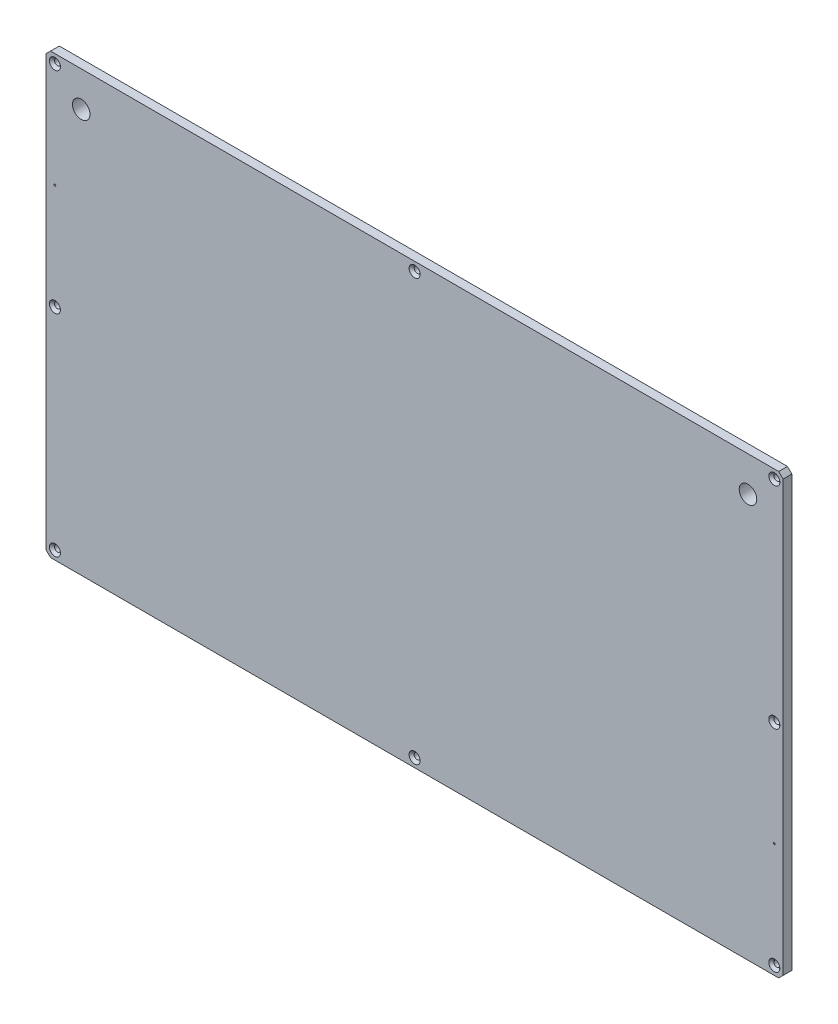
SolidWorks part; units mm, degrees
ref_plane "Front Plane" through (0, 0, 0) normal (0, 0, 1) x (1, 0, 0)
ref_plane "Top Plane" through (0, 0, 0) normal (0, 1, 0) x (1, 0, 0)
ref_plane "Right Plane" through (0, 0, 0) normal (1, 0, 0) x (0, 0, -1)
sketch "Sketch1" plane through (0, 0, 0) normal (0, 0, 1) x (1, 0, 0)
  line L1 (-20, -20) -> (400, -20)
  line L2 (-20, -20) -> (-20, 230)
  line L3 (-20, 230) -> (400, 230)
  line L4 (400, -20) -> (400, 230)
  dimension "D1" = 20
  dimension "D2" = 420
  dimension "D3" = 250
  dimension "D4" = 20
extrude "Boss-Extrude1" add sketch "Sketch1" against normal blind 10
chamfer "Chamfer1" distance 2.5 angle 45 4 edges at (400, 230, -5) (400, -20, -5) (-20, -20, -5) (-20, 230, -5)
ref_plane "Mid X Plane" through (190, 0, 0) normal (-1, 0, 0) x (0, 0, 1)
ref_plane "Mid Y Plane" through (0, 105, 0) normal (0, 1, 0) x (1, 0, 0)
sketch "Sketch8" plane through (0, 0, 0) normal (0, 0, 1) x (1, 0, 0)
  line L0 (400, -17.5) -> (400, 227.5) construction
  line L1 (0, 0) -> (380, 0)
  line L2 (0, 0) -> (0, 210)
  line L3 (0, 210) -> (380, 210)
  line L4 (380, 0) -> (380, 210)
  line L5 (397.5, 230) -> (-17.5, 230) construction
  dimension "D1" = 20
  dimension "D2" = 20
hole_wizard "CSK for M3 Flat Head Machine Screw2" positions "Sketch5" profile "Sketch6" countersink size "M3" standard "ANSI Metric"
sketch "Sketch5" plane through (0, 0, 0) normal (0, 0, 1) x (1, 0, 0)
  line L0 (-17.5, -20) -> (397.5, -20) construction
  line L1 (397.5, 230) -> (-17.5, 230) construction
  line L2 (-20, 227.5) -> (-20, -17.5) construction
  line L3 (400, -17.5) -> (400, 227.5) construction
  line L4 (190, 5.5) -> (190, -5.5) construction
  line L5 (5.5, 105) -> (-5.5, 105) construction
  point P0 (-15, 225)
  point P2 (190, 225)
  point P4 (395, 225)
  point P6 (395, -15)
  point P8 (190, -15)
  point P10 (-15, -15)
  point P29 (-15, 105)
  point P31 (395, 105)
  dimension "D1" = 5
  dimension "D2" = 5
  dimension "D3" = 5
  dimension "D4" = 5
sketch "Sketch6" plane through (-15, 225, 0) normal (1, 0, 0) x (0, -1, 0)
  line L0 (0, 0) -> (0, 16.0215)
  line L1 (0, 16.0215) -> (1.7, 15)
  line L2 (1.7, 15) -> (1.7, 1.45)
  line L3 (1.7, 1.45) -> (3.15, 0)
  line L5 (3.15, 0) -> (0, 0)
  line L6 (-1.7, 1.45) -> (-3.15, 0) construction
  line L10 (0, 16.0215) -> (-1.7, 15) construction
  line L11 (0, -6.35) -> (0, 107.95) construction
  dimension "Hole Dia." = 3.4
  dimension "Hole Depth" = 15
  dimension "Near C'Sink Dia." = 6.3
  dimension "Near C'Sink Angle" = 90
  dimension "Drill Angle" = 118
sketch "Sketch7" plane through (0, 0, -10) normal (0, 0, -1) x (-1, 0, 0)
  line L0 (-190, -5.5) -> (-190, 5.5) construction
  line L1 (-390, 220) -> (10, 220)
  line L2 (-390, 220) -> (-390, -10)
  line L3 (-390, -10) -> (10, -10)
  line L4 (10, 220) -> (10, -10)
  line L5 (-390, 220) -> (10, -10) construction
  line L6 (-390, -10) -> (10, 220) construction
  line L7 (5.5, 105) -> (-5.5, 105) construction
  point P0 (-190, 105)
  dimension "D1" = 400
  dimension "D2" = 230
extrude "Cut-Extrude2" cut sketch "Sketch7" against normal blind 5 flip side to cut
chamfer "Chamfer2" distance 2.5 angle 45 4 edges at (-10, 220, -7.5) (-10, -10, -7.5) (390, -10, -7.5) (390, 220, -7.5)
hole_wizard "Ø10.0mm Dowel Hole1" positions "Sketch9" profile "Sketch10" hole size "Ø10.0" standard "ANSI Metric" end condition through all
sketch "Sketch9" plane through (0, 0, 0) normal (0, 0, 1) x (1, 0, 0)
  line L0 (190, 5.5) -> (190, -5.5) construction
  line L2 (5.5, 105) -> (-5.5, 105) construction
  point P0 (0, 210)
  dimension "D1" = 190
  dimension "D2" = 105
sketch "Sketch10" plane through (0, 210, 0) normal (1, 0, 0) x (0, -1, 0)
  line L0 (0, 0) -> (0, 10)
  line L1 (0, 10) -> (5, 10)
  line L2 (5, 10) -> (5, 0)
  line L5 (5, 0) -> (0, 0)
  line L11 (0, -6.35) -> (0, 107.95) construction
  dimension "Thru Hole Dia." = 10
  dimension "Thru Hole Depth" = 10
mirror "Mirror1" about plane through (190, 0, 0) normal (-1, 0, 0) of "Ø10.0mm Dowel Hole1"
hole_wizard "Ø1.0mm Dowel Hole1" positions "Sketch11" profile "Sketch12" hole size "Ø1.0" standard "ANSI Metric" end condition through all
sketch "Sketch11" plane through (0, 0, 0) normal (0, 0, 1) x (1, 0, 0)
  line L0 (-20, 227.5) -> (-20, -17.5) construction
  line L1 (400, -17.5) -> (400, 227.5) construction
  line L2 (2.75, 105) -> (-2.75, 105) construction
  point P0 (-15, 165)
  point P2 (395, 45)
  dimension "D1" = 5
  dimension "D2" = 5
  dimension "D3" = 60
  dimension "D4" = 60
sketch "Sketch12" plane through (-15, 165, 0) normal (1, 0, 0) x (0, -1, 0)
  line L0 (0, 0) -> (0, 10)
  line L1 (0, 10) -> (0.5, 10)
  line L2 (0.5, 10) -> (0.5, 0)
  line L5 (0.5, 0) -> (0, 0)
  line L11 (0, -6.35) -> (0, 107.95) construction
  dimension "Thru Hole Dia." = 1
  dimension "Thru Hole Depth" = 10
